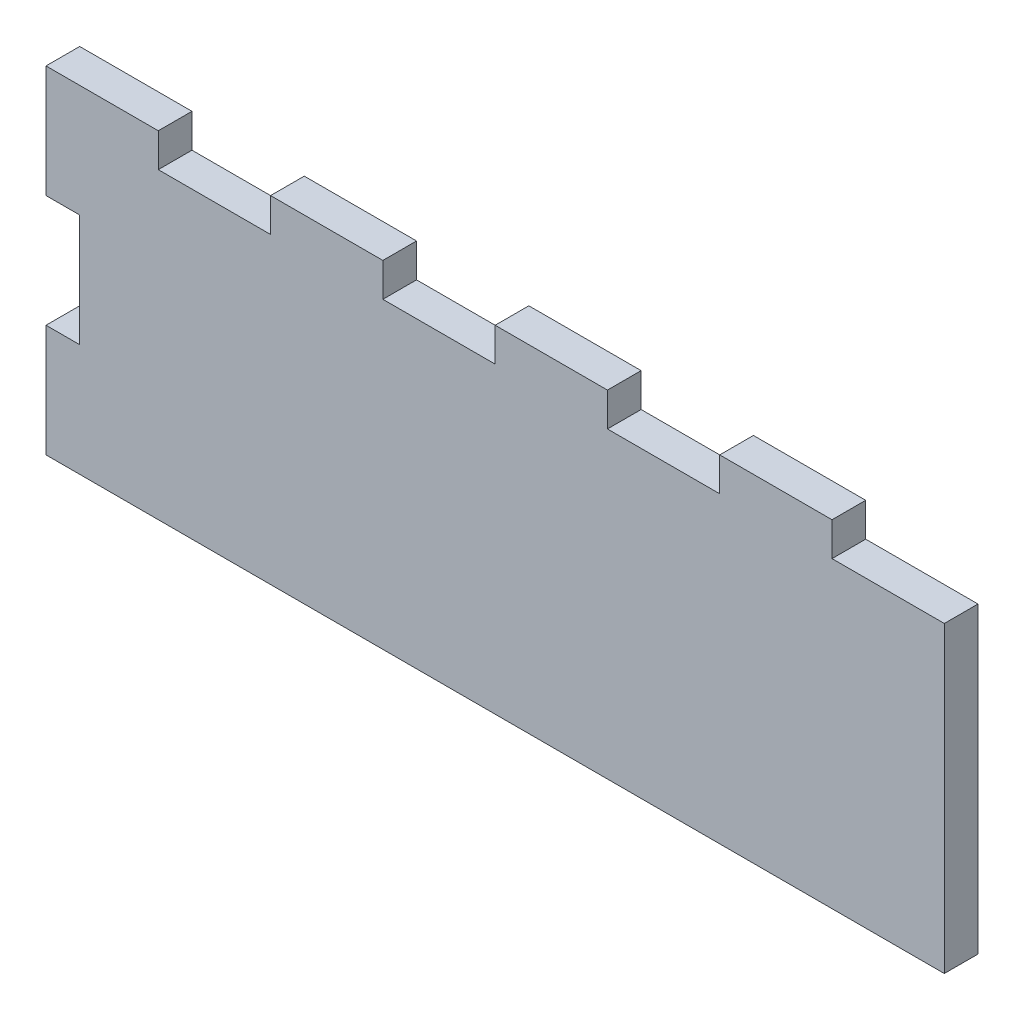
SolidWorks part; units mm, degrees
ref_plane "Plan de face" through (0, 0, 0) normal (0, 0, 1) x (1, 0, 0)
ref_plane "Plan de dessus" through (0, 0, 0) normal (0, 1, 0) x (1, 0, 0)
ref_plane "Plan de droite" through (0, 0, 0) normal (1, 0, 0) x (0, 0, -1)
sketch "Esquisse1" plane through (0, 0, 0) normal (0, 0, 1) x (1, 0, 0)
  line L1 (0, 0) -> (80, 0)
  line L2 (0, 0) -> (0, -30)
  line L3 (0, -30) -> (80, -30)
  line L4 (80, 0) -> (80, -30)
  dimension "D1" = 80
  dimension "D2" = 30
extrude "Boss.-Extru.1" add sketch "Esquisse1" along normal blind 3
sketch "Esquisse2" plane through (0, 0, 3) normal (0, 0, 1) x (1, 0, 0)
  line L1 (80, 0) -> (70, 0)
  line L2 (80, 0) -> (80, -3)
  line L3 (80, -3) -> (70, -3)
  line L4 (70, 0) -> (70, -3)
  dimension "D1" = 10
  dimension "D2" = 3
extrude "Enlèv. mat.-Extru.1" cut sketch "Esquisse2" against normal blind 3
pattern_linear "Répétition linéaire1" count 4 spacing 20 along (-1, 0, 0) of "Enlèv. mat.-Extru.1"
sketch "Esquisse3" plane through (0, 0, 0) normal (0, 0, -1) x (-1, 0, 0)
  line L0 (0, 0) -> (0, -30) construction
  line L5 (0, -20) -> (-3, -20)
  line L6 (0, -20) -> (0, -10)
  line L7 (0, -10) -> (-3, -10)
  line L8 (-3, -20) -> (-3, -10)
  line L9 (0, -30) -> (-80, -30) construction
  dimension "D1" = 3
  dimension "D2" = 10
  dimension "D3" = 10
extrude "Enlèv. mat.-Extru.2" cut sketch "Esquisse3" against normal blind 3
